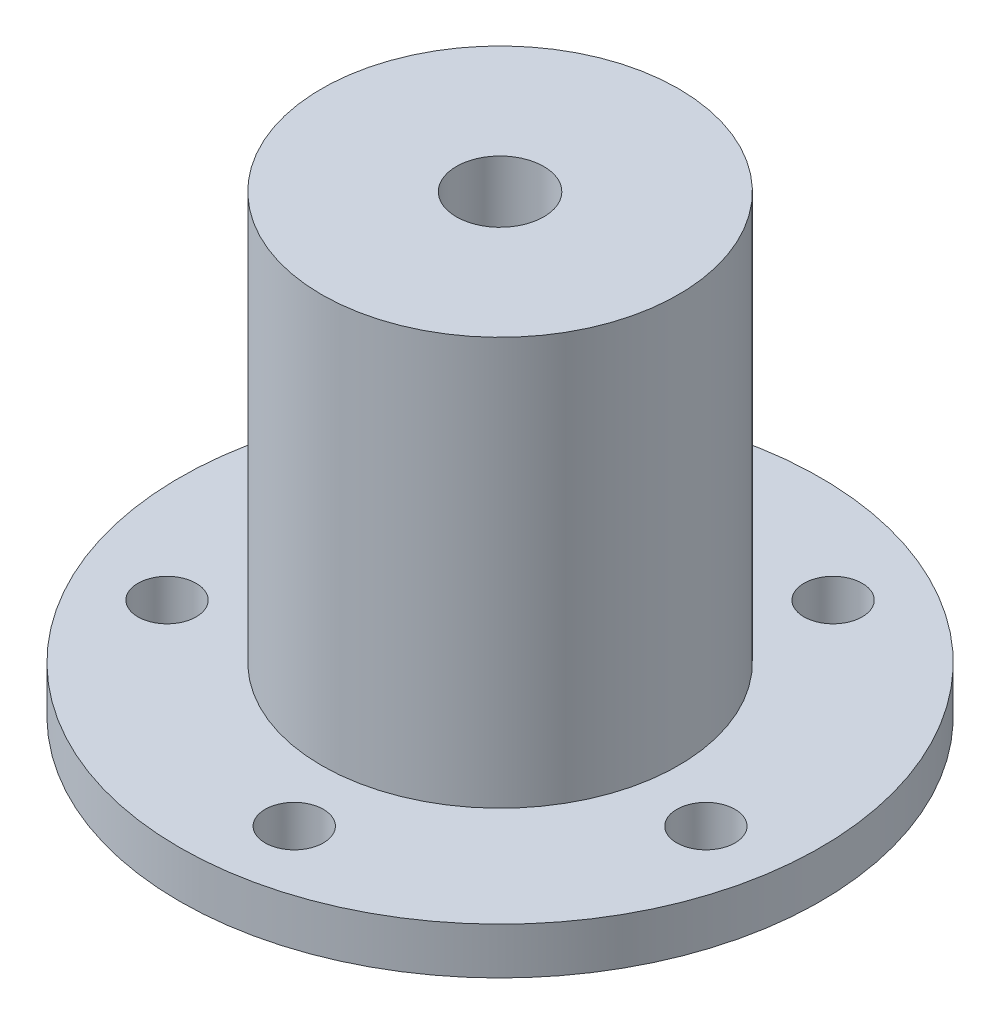
SolidWorks part; units mm, degrees
ref_plane "Ebene vorne" through (0, 0, 0) normal (0, 0, 1) x (1, 0, 0)
ref_plane "Ebene oben" through (0, 0, 0) normal (0, 1, 0) x (1, 0, 0)
ref_plane "Ebene rechts" through (0, 0, 0) normal (1, 0, 0) x (0, 0, -1)
sketch "Skizze1" plane through (0, 0, 0) normal (0, 1, 0) x (1, 0, 0)
  circle A0 centre (0, 0) radius 11
  dimension "D1" = 22
extrude "Aufsatz-Linear austragen1" add sketch "Skizze1" along normal blind 1.6
sketch "Skizze2" plane through (0, 1.6, 0) normal (0, 1, 0) x (1, 0, 0)
  circle A0 centre (0, 0) radius 6.125
  dimension "D1" = 12.25
extrude "Aufsatz-Linear austragen2" add sketch "Skizze2" along normal blind 14
sketch "Skizze3" plane through (0, 15.6, 0) normal (0, 1, 0) x (1, 0, 0)
  circle A0 centre (0, 0) radius 1.5
  point P4 (0, 0)
  dimension "D1" = 3
extrude "Schnitt-Linear austragen1" cut sketch "Skizze3" against normal through all
sketch "Skizze4" plane through (0, 15.6, 0) normal (0, 1, 0) x (1, 0, 0)
  point P0 (0, 0)
sketch "Skizze5" plane through (0, 0, 0) normal (0, 0, 1) x (1, 0, 0)
  line L0 (6.125, 15.6) -> (-6.125, 15.6) construction
  circle A0 centre (0, 10.6) radius 0.8308
  point P5 (0, 10.6)
  point P6 (0, 10.6)
  point P7 (0, 10.6)
  dimension "D1" = 5
extrude "Schnitt-Linear austragen3" cut sketch "Skizze5" against normal through all
sketch "Skizze7" plane through (0, 0, 0) normal (0, 0, 1) x (1, 0, 0)
  circle A0 centre (0, 10.6) radius 1.5
  point P0 (0, 10.6)
  dimension "D1" = 3
sketch "Skizze8" plane through (0, 0, 0) normal (0, -1, 0) x (1, 0, 0)
  line L9 (-5.5, 5.5) -> (-8.734, 8.734) construction
  circle A0 centre (0, 0) radius 11 construction
  circle A6 centre (-6.0104, -6.0104) radius 1
  circle A7 centre (-7.5736, 3.8589) radius 1
  circle A8 centre (1.3297, 8.3954) radius 1
  circle A9 centre (8.3954, 1.3297) radius 1
  circle A10 centre (3.8589, -7.5736) radius 1
  point P33 (0, 0)
  dimension "D2" = 2
  dimension "D3" = 8.5
  dimension "D1" = 5
extrude "Schnitt-Linear austragen4" cut sketch "Skizze8" against normal up to surface (1.6 mm away) up to face at (0, 1.6, 6.125)
extrude "Schnitt-Linear austragen5" cut sketch "Skizze7" against normal blind 10
